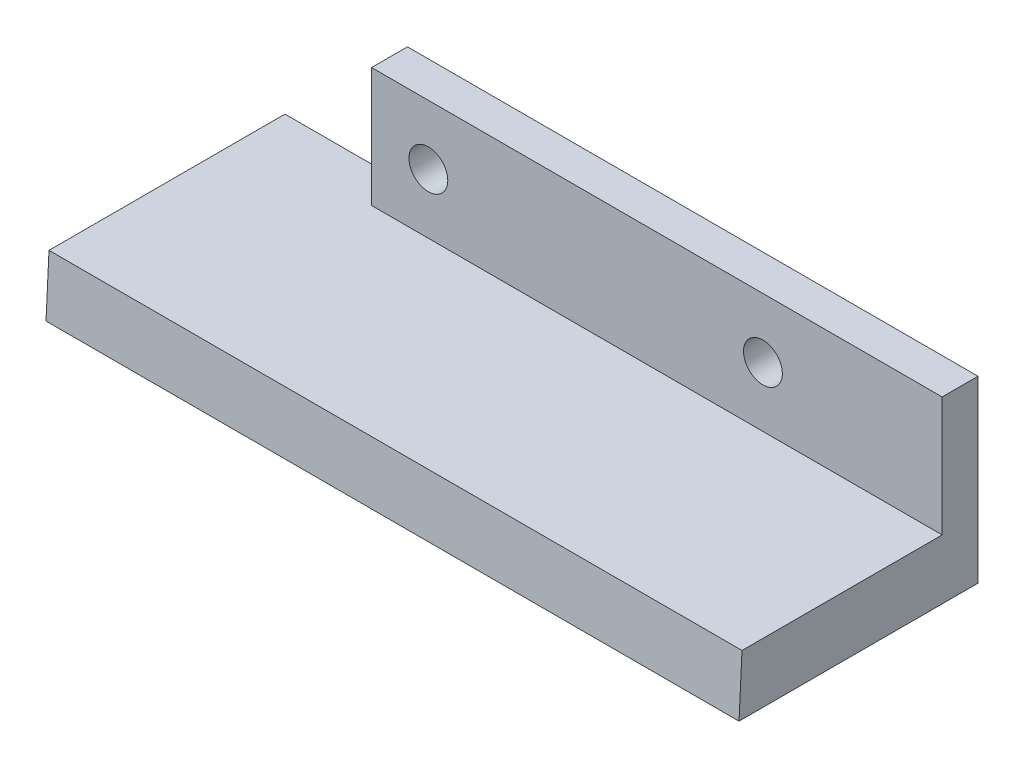
SolidWorks part; units mm, degrees
ref_plane "Plan de face" through (0, 0, 0) normal (0, 0, 1) x (1, 0, 0)
ref_plane "Plan de dessus" through (0, 0, 0) normal (0, 1, 0) x (1, 0, 0)
ref_plane "Plan de droite" through (0, 0, 0) normal (1, 0, 0) x (0, 0, -1)
sketch "Esquisse1" plane through (0, 0, 0) normal (0, 0, 1) x (1, 0, 0)
  line L1 (0, 0) -> (58, 0)
  line L2 (0, 0) -> (0, -5)
  line L3 (0, -5) -> (58, -5)
  line L4 (58, 0) -> (58, -5)
  dimension "D1" = 58
  dimension "D2" = 5
extrude "Boss.-Extru.1" add sketch "Esquisse1" along normal blind 20
sketch "Esquisse3" plane through (0, 0, 0) normal (0, 1, 0) x (1, 0, 0)
  line L1 (58, 0) -> (10.25, 0)
  line L2 (58, 0) -> (58, -3)
  line L3 (58, -3) -> (10.25, -3)
  line L4 (10.25, 0) -> (10.25, -3)
  dimension "D1" = 47.75
  dimension "D2" = 3
extrude "Boss.-Extru.2" add sketch "Esquisse3" along normal blind 10
sketch "Esquisse4" plane through (0, 0, 3) normal (0, 0, 1) x (1, 0, 0)
  line L1 (58, 10) -> (58, 0) construction
  circle A0 centre (43, 5) radius 1.625
  circle A1 centre (15, 5) radius 1.625
  point P7 (58, 5)
  dimension "D1" = 3.25
  dimension "D2" = 3.25
  dimension "D3" = 28
  dimension "D4" = 15
extrude "Enlèv. mat.-Extru.1" cut sketch "Esquisse4" against normal blind 10
sketch "Esquisse6" plane through (58, 0, 0) normal (1, 0, 0) x (0, 0, -1)
  line L0 (-20, -5) -> (-19.75, 0)
  line L1 (-20, 0) -> (-3, 0) construction
  line L2 (-19.75, 0) -> (-20, 0)
  line L3 (-20, 0) -> (-20, -5)
  dimension "D1" = 0.25
extrude "Enlèv. mat.-Extru.2" cut sketch "Esquisse6" against normal through all
